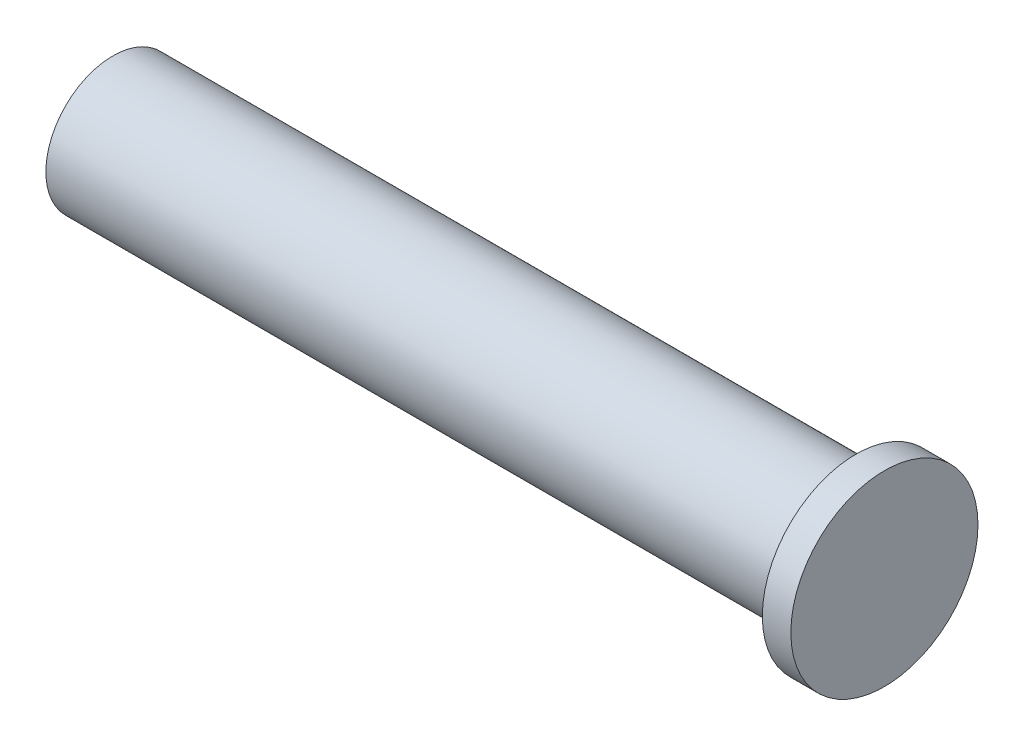
SolidWorks part; units mm, degrees
ref_plane "Front Plane" through (0, 0, 0) normal (0, 0, 1) x (1, 0, 0)
ref_plane "Top Plane" through (0, 0, 0) normal (0, 1, 0) x (1, 0, 0)
ref_plane "Right Plane" through (0, 0, 0) normal (1, 0, 0) x (0, 0, -1)
sketch "Sketch2" plane through (0, 0, 0) normal (0, 1, 0) x (1, 0, 0)
  line L0 (-22.6695, -3.937) -> (20.9931, -3.937)
  line L1 (20.9931, -3.937) -> (20.9931, -5.4991)
  line L2 (20.9931, -5.4991) -> (22.6695, -5.4991)
  line L3 (22.6695, -5.4991) -> (22.6695, 0)
  line L4 (22.6695, 0) -> (-22.6695, 0)
  line L5 (-22.6695, 0) -> (-22.6695, -3.937)
  point P0 (0, 0)
  dimension "D1" = 1.6764
  dimension "D2" = 45.339
  dimension "D3" = 3.937
  dimension "D4" = 5.4991
revolve "Revolve1" add sketch "Sketch2" angle 360 about L4
